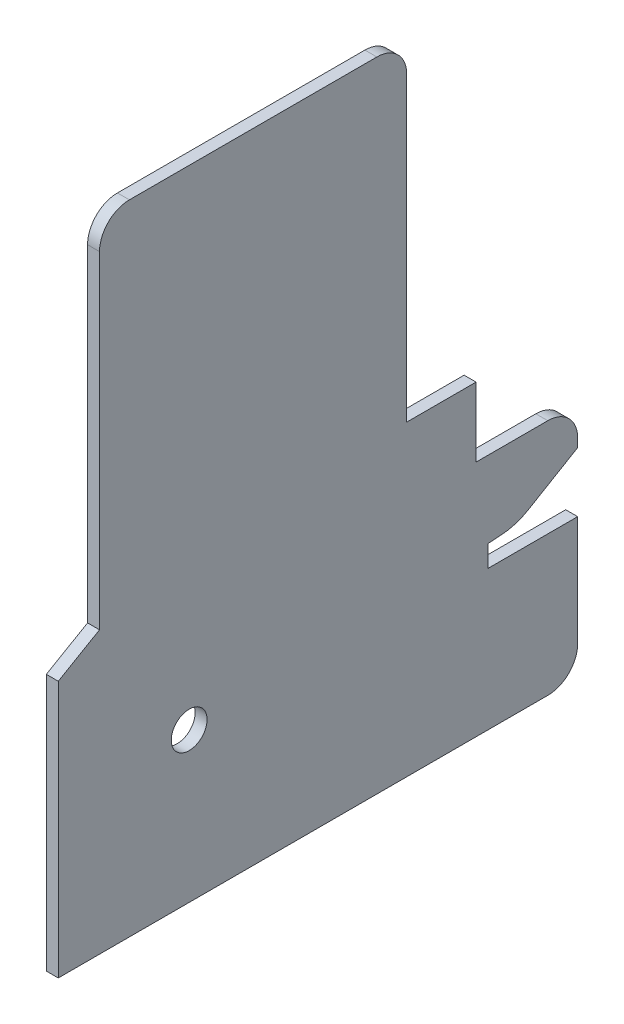
SolidWorks part; units mm, degrees
ref_plane "Ebene vorne" through (0, 0, 0) normal (0, 0, 1) x (1, 0, 0)
ref_plane "Ebene oben" through (0, 0, 0) normal (0, 1, 0) x (1, 0, 0)
ref_plane "Ebene rechts" through (0, 0, 0) normal (1, 0, 0) x (0, 0, -1)
sketch "Skizze2" plane through (0, 0, 0) normal (1, 0, 0) x (0, 0, -1)
  line L0 (0, 0) -> (-86.9, 0)
  line L1 (-86.9, 0) -> (-86.9, 43)
  line L2 (-86.9, 43) -> (-80, 47)
  line L3 (-80, 47) -> (-80, 106.8)
  line L4 (-80, 106.8) -> (-28.6, 106.8)
  line L5 (-28.6, 106.8) -> (-28.6, 51.3961)
  line L6 (-28.6, 51.3961) -> (-17, 51.3961)
  line L7 (-17, 51.3961) -> (-17, 39.8)
  line L8 (-17, 39.8) -> (0, 39.8)
  line L9 (0, 39.8) -> (0, 33.4)
  line L10 (0, 33.4) -> (-10.3339, 27.3)
  line L11 (-10.3339, 27.3) -> (-15, 27)
  line L12 (-15, 27) -> (-15, 23.4)
  line L13 (-15, 23.4) -> (0, 23.4)
  line L14 (0, 23.4) -> (0, 0)
  dimension "D1" = 106.8
  dimension "D2" = 86.9
  dimension "D3" = 51.3961
  dimension "D4" = 47
  dimension "D5" = 43
  dimension "D6" = 80
  dimension "D7" = 28.6
  dimension "D8" = 17
  dimension "D9" = 39.8
  dimension "D10" = 3.6
  dimension "D11" = 23.4
  dimension "D12" = 0.3
  dimension "D13" = 12
  dimension "D14" = 6.4
  dimension "D15" = 15
extrude "Aufsatz-Linear austragen1" add sketch "Skizze2" against normal blind 2
fillet "Verrundung6" radius 5 4 edges at (-1, 0, 0) (-1, 39.8, 0) (-1, 106.8, 80) (-1, 106.8, 28.6)
fillet "Verrundung7" radius 10 1 edges at (-1, 27.3, 10.3339)
sketch "Skizze4" plane through (0, 0, 0) normal (1, 0, 0) x (0, 0, -1)
  line L1 (-65, 22) -> (-65, 31.0007) construction
  line L2 (-62, 25) -> (-68, 25) construction
  circle A0 centre (-65, 25) radius 3
  point P0 (-65, 22)
  point P1 (-62, 25)
  point P7 (-65, 25)
  point P8 (-65, 25)
  dimension "D2" = 6
  dimension "D1" = 22
  dimension "D3" = 62
  dimension "D4" = 65
extrude "Schnitt-Linear austragen1" cut sketch "Skizze4" against normal up to surface (2 mm away) up to face at (-2, 44.7031, 29.6222)
